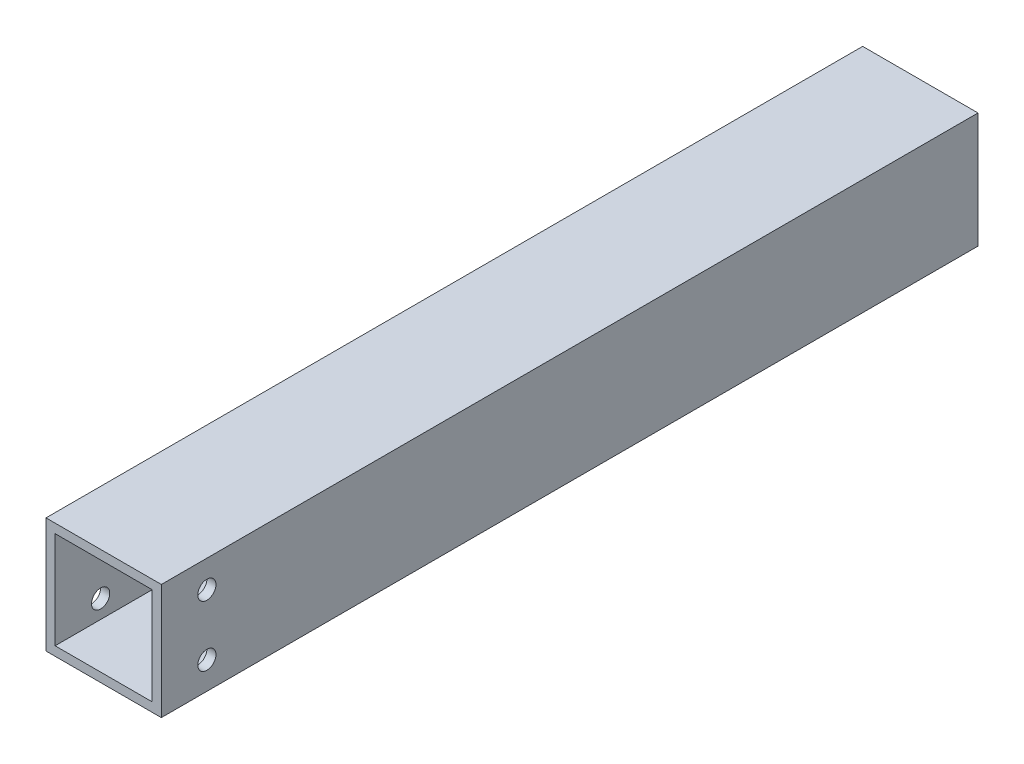
SolidWorks part; units mm, degrees
material "6061-T6 (SS)"
ref_plane "Front Plane" through (0, 0, 0) normal (0, 0, 1) x (1, 0, 0)
ref_plane "Top Plane" through (0, 0, 0) normal (0, 1, 0) x (1, 0, 0)
ref_plane "Right Plane" through (0, 0, 0) normal (1, 0, 0) x (0, 0, -1)
sketch "Sketch1" plane through (0, 0, 0) normal (0, 0, 1) x (1, 0, 0)
  line L0 (-16, 16) -> (16, 16)
  line L1 (-19, -19) -> (19, -19)
  line L2 (-19, -19) -> (-19, 19)
  line L3 (-19, 19) -> (19, 19)
  line L4 (19, -19) -> (19, 19)
  line L5 (-19, -19) -> (19, 19) construction
  line L6 (-19, 19) -> (19, -19) construction
  line L7 (16, -16) -> (16, 16)
  line L8 (-16, -16) -> (16, -16)
  line L9 (-16, -16) -> (-16, 16)
  point P0 (0, 0)
  dimension "D1" = 38
  dimension "D2" = 38
  dimension "D3" = 3
extrude "Boss-Extrude1" add sketch "Sketch1" along normal blind 269.06
sketch "Sketch2" plane through (19, 0, 0) normal (1, 0, 0) x (0, 0, -1)
  line L0 (-254.06, 19) -> (-254.06, -19) construction
  line L1 (-269.06, 19) -> (0, 19) construction
  line L2 (-269.06, -19) -> (0, -19) construction
  circle A0 centre (-254.06, 10) radius 3
  circle A1 centre (-254.06, -10) radius 3
  point P10 (-254.06, 0)
  dimension "D1" = 6
  dimension "D2" = 6
  dimension "D4" = 10
  dimension "D3" = 20
  dimension "D5" = 15
extrude "Cut-Extrude1" cut sketch "Sketch2" against normal through all both and the other way through all
